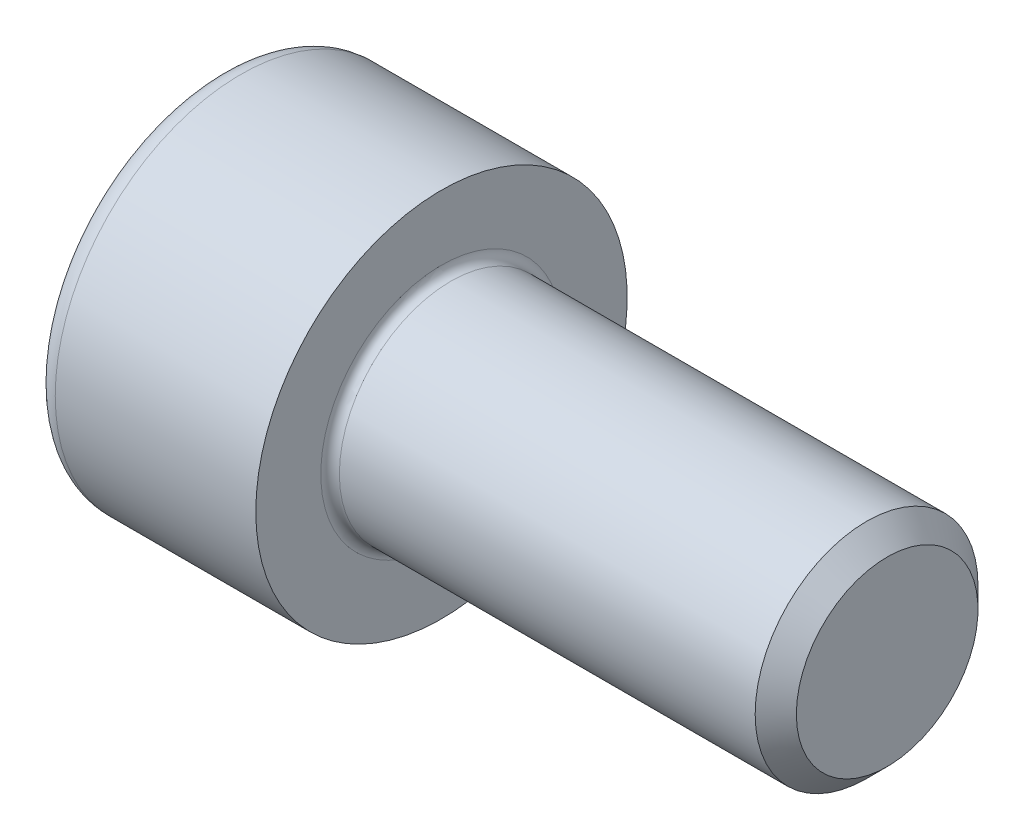
SolidWorks part; units mm, degrees
ref_plane "Plane1" through (0, 0, 0) normal (0, 0, 1) x (1, 0, 0)
ref_plane "Plane2" through (0, 0, 0) normal (0, 1, 0) x (1, 0, 0)
ref_plane "Plane3" through (0, 0, 0) normal (1, 0, 0) x (0, 0, -1)
sketch "BodySke" plane through (0, 0, 0) normal (0, 0, 1) x (1, 0, 0)
  line L0 (0, 0) -> (0, 5)
  line L1 (0, 5) -> (6, 5)
  line L2 (6, 5) -> (6, 3)
  line L3 (6, 3) -> (17.4455, 3)
  line L4 (18, 2.4455) -> (18, 0)
  line L5 (18, 0) -> (0, 0)
  line L6 (-31.75, 0) -> (127, 0) construction
  line L8 (18, 2.4455) -> (17.4455, 3)
  line L10 (18, -2.4455) -> (17.4455, -3) construction
  line L11 (7, 9.525) -> (7, 3.175) construction
  line L12 (6, 9.525) -> (6, 3.175) construction
  line L13 (-42, 9.525) -> (-42, 3.175) construction
  dimension "Diameter" = 6
  dimension "Head_ht" = 6
  dimension "Length" = 12
  dimension "Body_ch_ang" = 45
  dimension "Head_dia" = 10
  dimension "Minor_dia" = 4.891
  dimension "Advance" = 1
  dimension "Thread_nom" = 12
  dimension "Thread_length" = 60
revolve "Base-Revolve" add sketch "BodySke"
cosmetic thread "ThreadCosmetic" [suppressed]
fillet "Fillet1" radius 0.25 1 edges at (6, 0, 3)
fillet "Fillet2" radius 0.6 1 edges at (0, 0, 5)
sketch "Sketch2" plane through (0, 0, 0) normal (0, 0, 1) x (1, 0, 0)
  line L0 (0, 2.51) -> (3, 2.51)
  line L1 (3, 2.51) -> (4.4491, 0)
  line L2 (-31.75, 0) -> (127, 0) construction
  line L3 (4.4491, 0) -> (0, 0)
  line L4 (0, 0) -> (0, 2.51)
  line L6 (0, 0) -> (47.625, 0) construction
  dimension "D1" = 2.51
  dimension "D2" = 60
  dimension "Depth" = 3
revolve "Hex-PreBroach" cut sketch "Sketch2" angle 360 about L6
sketch "Sketch3" plane through (0, 0, 0) normal (-1, 0, 0) x (0, 0.5, 0.866)
  line L0 (1.4491, 2.51) -> (-1.4491, 2.51)
  line L1 (-1.4491, 2.51) -> (-2.8983, 0)
  line L2 (1.4491, 2.51) -> (2.8983, 0)
  line L3 (1.4491, -2.51) -> (2.8983, 0)
  line L4 (1.4491, -2.51) -> (-1.4491, -2.51)
  line L5 (-1.4491, -2.51) -> (-2.8983, 0)
  dimension "D1" = 2.51
  dimension "D2" = 2.51
  dimension "Hex_size" = 5.02
extrude "Hex" cut sketch "Sketch3" against normal blind 3
sketch "ThdSchSke" plane through (0, 0, 0) normal (0, 0, 1) x (1, 0, 0)
  line L0 (9, -2.4455) -> (8.6117, -3)
  line L1 (9, -2.4455) -> (9.3883, -3)
  line L2 (9.3883, -3) -> (9.3883, -3.75)
  line L3 (-3.175, 0) -> (5.1513, 0) construction
  line L4 (0, 4.4) -> (0, -4.4) construction
  line L5 (9.3883, -3.75) -> (8.6117, -3.75)
  line L6 (8.6117, -3.75) -> (8.6117, -3)
  dimension "Thread_minor" = 4.891
  dimension "Diameter" = 6
  dimension "Start" = 9
  dimension "SideAngle" = 55
  dimension "VeeAngle" = 70
  dimension "Overcut" = 7.5
revolve "ThreadSchematic" [suppressed] cut sketch "ThdSchSke" angle 360 about L3
pattern_linear "ThdSchPat" [suppressed]
equation "\"D2@Sketch3\" = \"Hex_size@Sketch3\" / 2"
equation "\"D1@Sketch3\" = \"Hex_size@Sketch3\" / 2"
equation "\"D1@Sketch2\" = \"Hex_size@Sketch3\" / 2"
equation "\"Thread_minor@ThreadCosmetic\"  =  \"Minor_dia@BodySke\""
equation "\"Depth@Sketch2\" =  \"Key_eng@Hex\""
equation "\"Thread_length@ThreadCosmetic\" = ((sgn( (\"Length@BodySke\" - \"Advance@BodySke\" * 3.0) - \"Thread_nom@BodySke\" )-1)*( (\"Length@BodySke\" - \"Advance@BodySke\" * 3.0) - \"Thread_nom@BodySke\" ))/-2+ \"Thread_nom@BodySke\""
equation "\"Thread_minor@ThdSchSke\" = \"Minor_dia@BodySke\""
equation "\"Diameter@ThdSchSke\" = \"Diameter@BodySke\""
equation "\"Overcut@ThdSchSke\" = \"Diameter@BodySke\" * 1.25"
equation "\"Start@ThdSchSke\" = \"Head_ht@BodySke\" + \"Length@BodySke\" - \"Thread_length@ThreadCosmetic\"  '---Non-countersunk---"
equation "\"Num_threads@ThdSchPat\" = int( \"Thread_length@ThreadCosmetic\" / \"Advance@BodySke\" + 0.999 )  + 1"
equation "\"Advance@ThdSchPat\" = \"Thread_length@ThreadCosmetic\" /  (\"Num_threads@ThdSchPat\" - 1) 'relax it"
equation "\"Num_threads@ThdSchPat\" = \"Num_threads@ThdSchPat\" - sgn( \"Num_threads@ThdSchPat\" - 1) '---chamfered tips only---"
